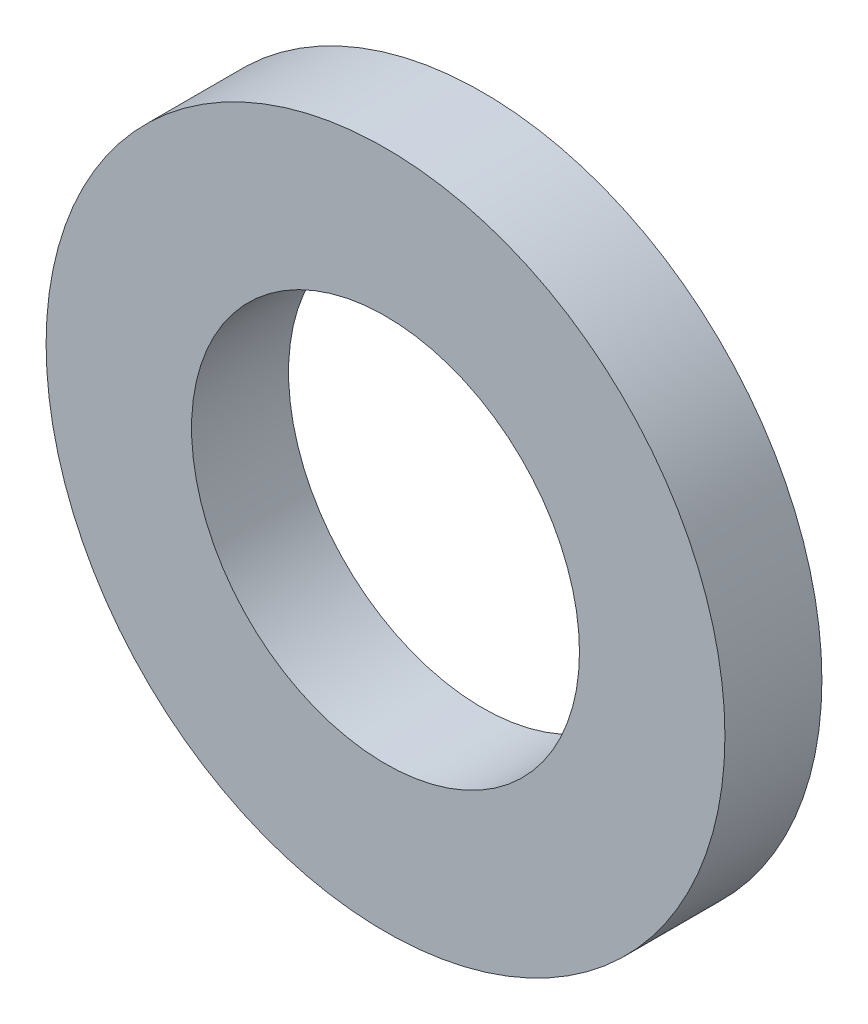
SolidWorks part; units mm, degrees
ref_plane "Front Plane" through (0, 0, 0) normal (0, 0, 1) x (1, 0, 0)
ref_plane "Top Plane" through (0, 0, 0) normal (0, 1, 0) x (1, 0, 0)
ref_plane "Right Plane" through (0, 0, 0) normal (1, 0, 0) x (0, 0, -1)
sketch "Sketch1" plane through (0, 0, 0) normal (0, 0, 1) x (1, 0, 0)
  circle A0 centre (0, 0) radius 4
  circle A1 centre (0, 0) radius 7
  dimension "D1" = 8
  dimension "D2" = 14
extrude "Boss-Extrude1" add sketch "Sketch1" along normal blind 2
